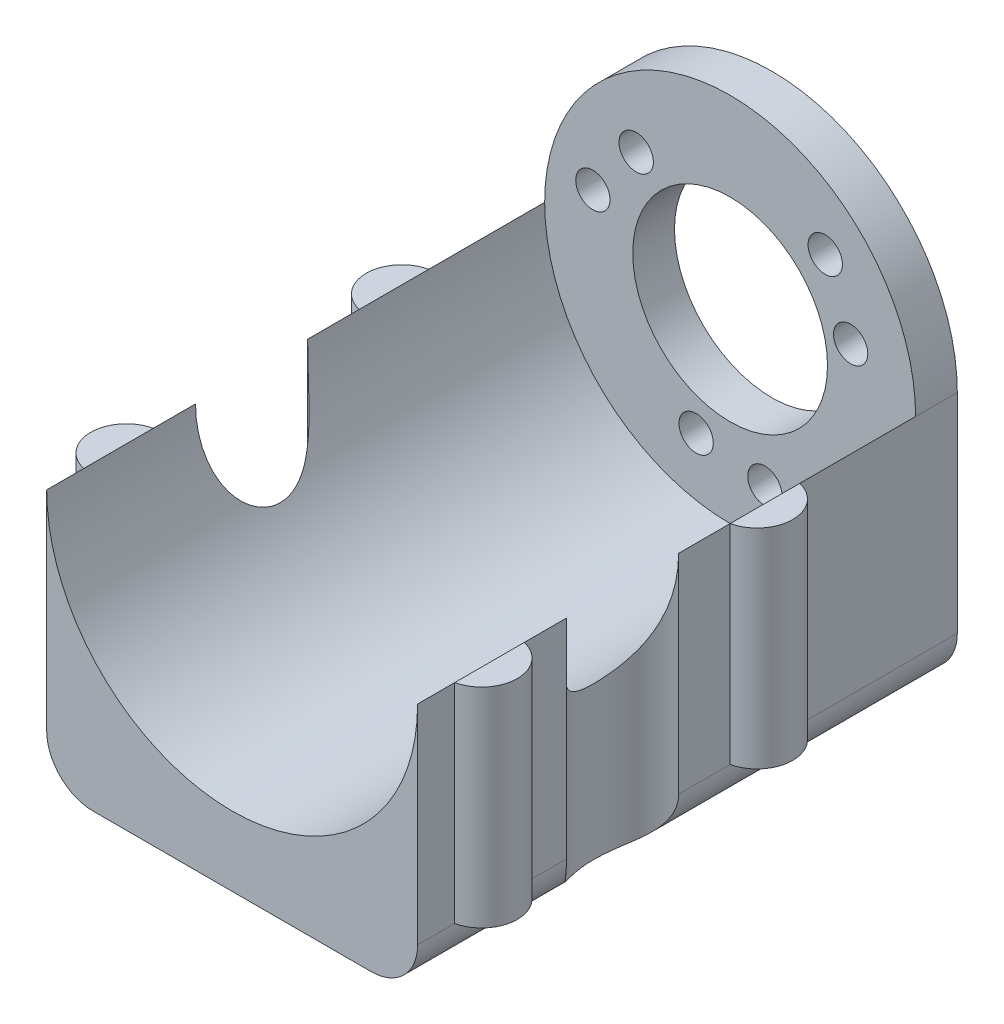
SolidWorks part; units mm, degrees
ref_plane "Front Plane" through (0, 0, 0) normal (0, 0, 1) x (1, 0, 0)
ref_plane "Top Plane" through (0, 0, 0) normal (0, 1, 0) x (1, 0, 0)
ref_plane "Right Plane" through (0, 0, 0) normal (1, 0, 0) x (0, 0, -1)
sketch "Sketch3" plane through (0, 0, 0) normal (0, 1, 0) x (1, 0, 0)
  line L0 (0, 0) -> (0, 53.7)
  line L1 (0, 53.7) -> (40, 53.7)
  line L2 (40, 53.7) -> (40, 0)
  line L3 (40, 0) -> (0, 0)
  dimension "D1" = 40
  dimension "D2" = 53.7
extrude "Boss-Extrude1" add sketch "Sketch3" along normal blind 27.5
sketch "Sketch4" plane through (0, 27.5, 0) normal (0, 1, 0) x (1, 0, 0)
  line L1 (0, 53.7) -> (0, 0) construction
  line L2 (0, 41.2) -> (0, 33.7)
  line L3 (0, 11.5) -> (0, 4)
  line L6 (40, 0) -> (40, 53.7) construction
  line L7 (40, 41.2) -> (40, 33.7)
  line L8 (40, 11.5) -> (40, 4)
  arc A4 (0, 33.7) -> (0, 41.2) centre (0.8438, 37.45) cw
  arc A5 (0, 4) -> (0, 11.5) centre (0.8438, 7.75) cw
  arc A7 (40, 33.7) -> (40, 41.2) centre (39.1562, 37.45) ccw
  arc A8 (40, 4) -> (40, 11.5) centre (39.1562, 7.75) ccw
  dimension "D3" = 12.5
  dimension "D6" = 4
  dimension "D8" = 0.8438
  dimension "D1" = 0.8438
  dimension "D4" = 0.8438
  dimension "D9" = 3.8438
  dimension "D12" = 3.8438
  dimension "D13" = 3.8438
  dimension "D2" = 0
  dimension "D5" = 7.5
  dimension "D7" = 0
  dimension "D10" = 0
  dimension "D11" = 12.5
  dimension "D14" = 0.8438
  dimension "D15" = 0
  dimension "D16" = 4
extrude "Boss-Extrude4" add sketch "Sketch4" against normal blind 27.5
sketch "Sketch6" plane through (0, 27.5, 0) normal (0, 1, 0) x (1, 0, 0)
  line L0 (0, 28.15) -> (0, 16.05)
  line L1 (0, 33.7) -> (0, 11.5) construction
  line L2 (40, 28.15) -> (40, 16.05)
  line L3 (40, 11.5) -> (40, 33.7) construction
  arc A0 (0, 16.05) -> (0, 28.15) centre (-4.3536, 22.1) ccw
  arc A2 (40, 16.05) -> (40, 28.15) centre (44.3536, 22.1) cw
  dimension "D2" = 7.4536
  dimension "D6" = 7.4536
  dimension "D1" = 12.1
  dimension "D3" = 0
  dimension "D4" = 5.55
  dimension "D5" = 12.1
  dimension "D7" = 0
  dimension "D8" = 5.55
extrude "Cut-Extrude1" cut sketch "Sketch6" against normal through all
sketch "Sketch7" plane through (0, 0, -53.7) normal (0, 0, -1) x (-1, 0, 0)
  line L1 (-40, 27.5) -> (0, 27.5) construction
  circle A2 centre (-20, 27.5) radius 20
  dimension "D1" = 40
extrude "Cut-Extrude2" cut sketch "Sketch7" against normal through all
sketch "Sketch8" plane through (0, 0, -53.7) normal (0, 0, -1) x (-1, 0, 0)
  line L4 (-40, 27.5) -> (-40, 0)
  line L5 (-40, 0) -> (0, 0)
  line L6 (0, 0) -> (0, 27.5)
  arc A1 (-40, 27.5) -> (0, 27.5) centre (-20, 27.5) cw
  dimension "D1" = 40
  dimension "D2" = 27.5
  dimension "D3" = 40
extrude "Boss-Extrude5" add sketch "Sketch8" along normal blind 4.5
sketch "Sketch9" plane through (0, 0, -58.2) normal (0, 0, -1) x (-1, 0, 0)
  circle A0 centre (-20, 27.5) radius 10.5
  dimension "D1" = 21
extrude "Cut-Extrude3" cut sketch "Sketch9" against normal through all
sketch "Sketch10" plane through (0, 0, -58.2) normal (0, 0, -1) x (-1, 0, 0)
  line L1 (-40, 0) -> (0, 0) construction
  line L2 (-30.2552, 37.7509) -> (-20, 27.5) construction
  line L3 (-40, 27.5) -> (-40, 0) construction
  line L5 (0, 0) -> (0, 27.5) construction
  circle A0 centre (-23.75, 12.9) radius 1.85
  circle A1 centre (-16.3338, 14.1) radius 1.85
  circle A3 centre (-32.9951, 30.7693) radius 1.85
  circle A4 centre (-30.2552, 37.7509) radius 1.85
  circle A5 centre (-9.87, 37.1194) radius 1.85
  circle A6 centre (-5.2, 31.2558) radius 1.85
  point P5 (0, 0)
  dimension "D2" = 3.7
  dimension "D3" = 3.7
  dimension "D5" = 3.7
  dimension "D6" = 3.7
  dimension "D11" = 3.7
  dimension "D12" = 3.7
  dimension "D14" = 13.4
  dimension "D4" = 16.25
  dimension "D8" = 12.9
  dimension "D9" = 16.3338
  dimension "D15" = 14.1
  dimension "D13" = 9.87
  dimension "D16" = 5.2
  dimension "D17" = 37.1194
  dimension "D18" = 31.2558
  dimension "D7" = 7.5
  dimension "D10" = 14.5
extrude "Cut-Extrude4" cut sketch "Sketch10" against normal through all
sketch "Sketch11" plane through (0, 0, 0) normal (0, 0, 1) x (1, 0, 0)
  line L1 (40, 0) -> (40, 27.5) construction
  line L4 (0, 0) -> (40, 0) construction
  line L5 (40, 5) -> (45.648, 5)
  line L6 (45.648, 5) -> (45.648, -3.0415)
  line L7 (45.648, -3.0415) -> (35, -3.0415)
  line L8 (35, 0) -> (35, -3.0415)
  arc A0 (35, 0) -> (40, 5) centre (35, 5) ccw
  point P12 (0, 0)
extrude "Cut-Extrude5" cut sketch "Sketch11" against normal through all
sketch "Sketch12" plane through (0, 0, 0) normal (0, 0, 1) x (1, 0, 0)
  line L8 (0, 5) -> (-3.9695, 5)
  line L9 (0, 0) -> (0, 27.5) construction
  line L10 (-3.9695, 5) -> (-3.9695, -1.478)
  line L11 (0, 0) -> (35, 0) construction
  line L12 (-3.9695, -1.478) -> (5, -1.478)
  line L13 (5, -1.478) -> (5, 0)
  arc A2 (0, 5) -> (5, 0) centre (5, 5) ccw
extrude "Cut-Extrude7" cut sketch "Sketch12" against normal through all
